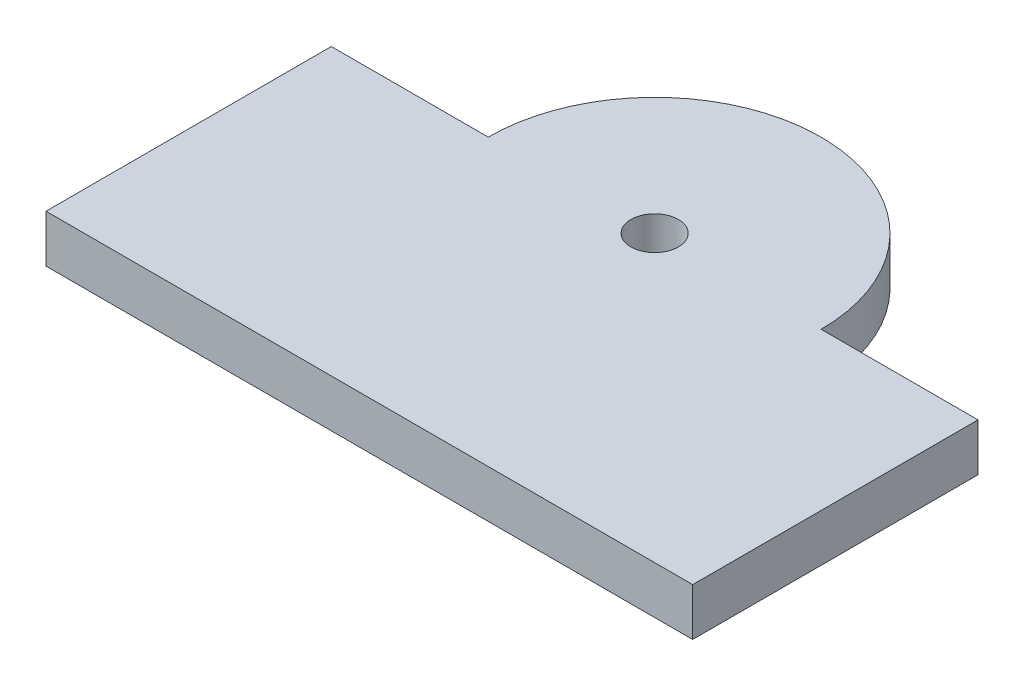
SolidWorks part; units mm, degrees
ref_plane "Front Plane" through (0, 0, 0) normal (0, 0, 1) x (1, 0, 0)
ref_plane "Top Plane" through (0, 0, 0) normal (0, 1, 0) x (1, 0, 0)
ref_plane "Right Plane" through (0, 0, 0) normal (1, 0, 0) x (0, 0, -1)
sketch "Sketch1" plane through (0, 0, 0) normal (0, 1, 0) x (1, 0, 0)
  line L1 (-34, -15) -> (34, -15)
  line L2 (-34, -15) -> (-34, 15)
  line L3 (-34, 15) -> (34, 15)
  line L4 (34, -15) -> (34, 15)
  line L5 (-34, -15) -> (34, 15) construction
  line L6 (-34, 15) -> (34, -15) construction
  point P0 (0, 0)
  dimension "D1" = 68
  dimension "D2" = 30
extrude "Boss-Extrude1" add sketch "Sketch1" along normal blind 5
sketch "Sketch2" plane through (0, 5, 0) normal (0, 1, 0) x (1, 0, 0)
  line L0 (0, -15) -> (0, 15) construction
  line L1 (-34, -15) -> (34, -15) construction
  line L2 (34, 15) -> (-34, 15) construction
  circle A0 centre (0, 15) radius 17.5
  dimension "D1" = 35
extrude "Boss-Extrude2" add sketch "Sketch2" against normal up to surface (5 mm away) up to face at (0, 0, 0)
sketch "Sketch3" plane through (0, 5, 0) normal (0, 1, 0) x (1, 0, 0)
  circle A0 centre (0, 15) radius 2.5
  arc A1 (17.5, 15) -> (-17.5, 15) centre (0, 15) ccw construction
  dimension "D1" = 5
extrude "Cut-Extrude1" cut sketch "Sketch3" against normal through all both and the other way through all
